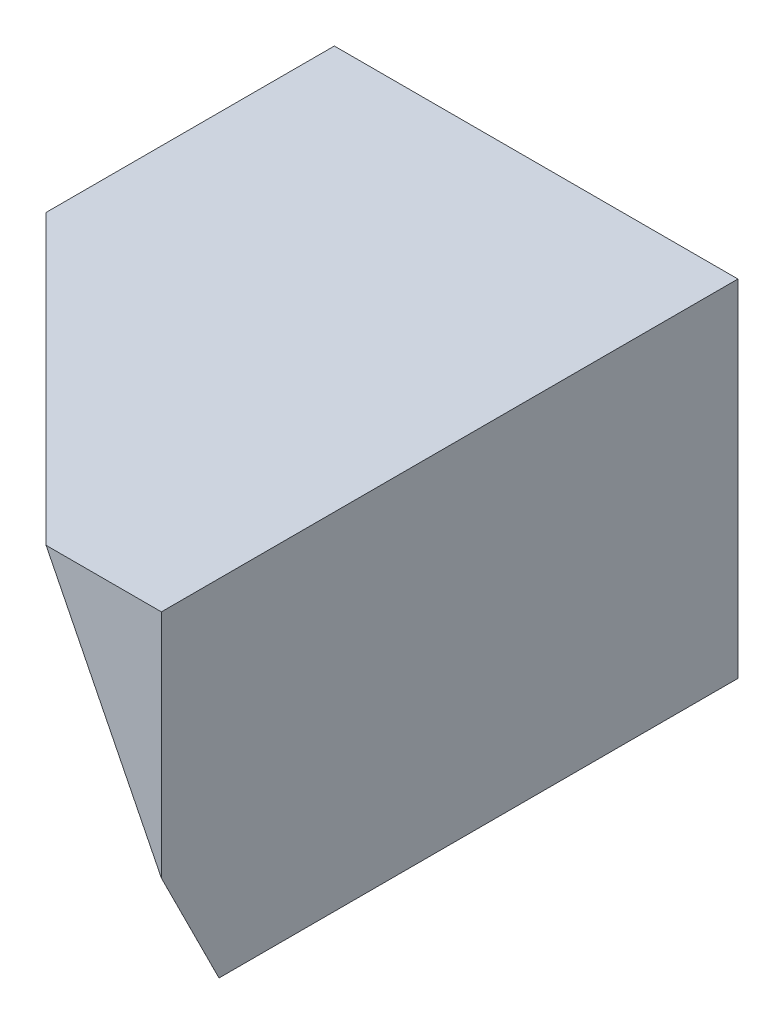
SolidWorks part; units mm, degrees
ref_plane "Front Plane" through (0, 0, 0) normal (0, 0, 1) x (1, 0, 0)
ref_plane "Top Plane" through (0, 0, 0) normal (0, 1, 0) x (1, 0, 0)
ref_plane "Right Plane" through (0, 0, 0) normal (1, 0, 0) x (0, 0, -1)
sketch "Sketch1" plane through (0, 0, 0) normal (0, 0, 1) x (1, 0, 0)
  line L0 (7, 0) -> (7, -6)
  line L1 (7, -6) -> (4, -6)
  line L2 (4, -6) -> (4, -7)
  line L3 (4, -7) -> (2, -7)
  line L4 (2, -7) -> (-1, -5)
  line L5 (-1, -5) -> (-1, -2)
  line L6 (-1, -2) -> (0, -2)
  line L7 (0, -2) -> (0, -4)
  line L8 (0, -4) -> (2, -4)
  line L9 (2, -4) -> (2, -2)
  line L10 (2, -2) -> (5, -2)
  line L11 (5, -2) -> (5, -6)
  line L12 (7, 0) -> (0, 0)
  line L13 (0, 0) -> (0, -2)
  line L14 (0, 0) -> (0, -2)
  dimension "D1" = 7
  dimension "D2" = 6
  dimension "D3" = 2
  dimension "D4" = 1
  dimension "D5" = 1
  dimension "D6" = 2
  dimension "D7" = 3
  dimension "D8" = 2
  dimension "D9" = 3
  dimension "D10" = 4
  dimension "D11" = 2
  dimension "D12" = 4
extrude "Boss-Extrude1" add sketch "Sketch1" along normal mid plane 10 contours L12 L13 L7 L8 L9 L10 L11 L1 L0 | L11 L10 L9 L8 L7 L6 L5 L4 L3 L2 L1
sketch "Sketch2" plane through (0, 0, 5) normal (0, 0, 1) x (1, 0, 0)
  line L0 (5, -6) -> (5, -2)
  line L1 (7, -6) -> (4, -6) construction
  line L2 (5, -2) -> (2, -2)
  line L3 (2, -2) -> (2, -4)
  line L4 (2, -4) -> (0, -4)
  line L5 (0, -4) -> (0, -2)
  line L6 (0, -2) -> (-1, -2)
  line L7 (-1, -2) -> (-1, -5)
  line L8 (-1, -5) -> (2, -7)
  line L9 (2, -7) -> (4, -7)
  line L10 (4, -7) -> (4, -6)
  line L11 (4, -6) -> (5, -6)
  dimension "D1" = 2
  dimension "D2" = 2
  dimension "D3" = 2
  dimension "D4" = 3
extrude "Cut-Extrude1" cut sketch "Sketch2" against normal blind 8
sketch "Sketch4" plane through (0, -2, 0) normal (0, -1, 0) x (1, 0, 0)
  line L0 (5, 5) -> (0, 0)
  line L1 (0, -3) -> (0, 5) construction
  line L2 (5, 5) -> (0, 5)
  line L4 (0, 5) -> (0, 0)
  line L5 (2, 5) -> (2, 2)
  line L6 (2, -3) -> (2, 5) construction
  dimension "D1" = 3
extrude "Cut-Extrude5" cut sketch "Sketch4" against normal through all
sketch "Sketch5" plane through (0, -4, 0) normal (0, -1, 0) x (1, 0, 0)
  line L0 (2, 2) -> (0, 0)
  line L1 (0, 0) -> (0, 5)
  line L2 (0, -3) -> (0, 5) construction
  line L3 (0, 5) -> (2, 5)
  line L4 (2, 5) -> (2, 2)
extrude "Cut-Extrude6" cut sketch "Sketch5" against normal through all
sketch "Sketch7" plane through (0, 0, 0) normal (-1, 0, 0) x (0, 0, 1)
  line L0 (0, 0) -> (-2, -4)
  line L1 (0, 0) -> (-5, 0) construction
  line L2 (-3, -4) -> (0, -4) construction
  line L3 (-3, -6) -> (-3, -2) construction
  point P6 (-3, -4)
  dimension "D1" = 5
  dimension "D2" = 1
sketch "Sketch8" plane through (5, 0, 0) normal (-1, 0, 0) x (0, 0, 1)
  line L0 (4, -2) -> (2, -6)
  line L2 (-3, -2) -> (5, -2) construction
  line L3 (-3, -6) -> (5, -6) construction
  dimension "D1" = 1
  dimension "D2" = 5
ref_plane "Plane1" through (0, 0, 0) normal (-0.6667, -0.3333, 0.6667) x (0.5963, 0.2981, 0.7454)
sketch "Sketch9" plane through (0, 0, 0) normal (-0.6667, -0.3333, 0.6667) x (0.5963, 0.2981, 0.7454)
  line L0 (0, 0) -> (-2.6833, -3.5777)
  line L1 (-2.6833, -3.5777) -> (4.8294, -9.2122)
  line L2 (4.8294, -9.2122) -> (9.3908, -3.1303)
  line L3 (9.3908, -3.1303) -> (0, 0)
  line L4 (6.7082, -2.2361) -> (0, 0) construction
  line L5 (5.3666, -4.0249) -> (2.6833, -7.6026) construction
  dimension "D1" = 7.6024
extrude "Cut-Extrude7" cut sketch "Sketch9" along normal blind 10
sketch "Sketch10" plane through (7, 0, 0) normal (1, 0, 0) x (0, 0, -1)
  line L0 (-4, -6) -> (-5, -6)
  line L1 (-5, -6) -> (5, -6) construction
  line L2 (-5, -6) -> (-5, -3.999)
  line L3 (-5, 0) -> (-5, -6) construction
  line L4 (-5, -3.999) -> (-4, -6)
  dimension "D1" = 1
extrude "Cut-Extrude10" cut sketch "Sketch10" against normal blind 1
